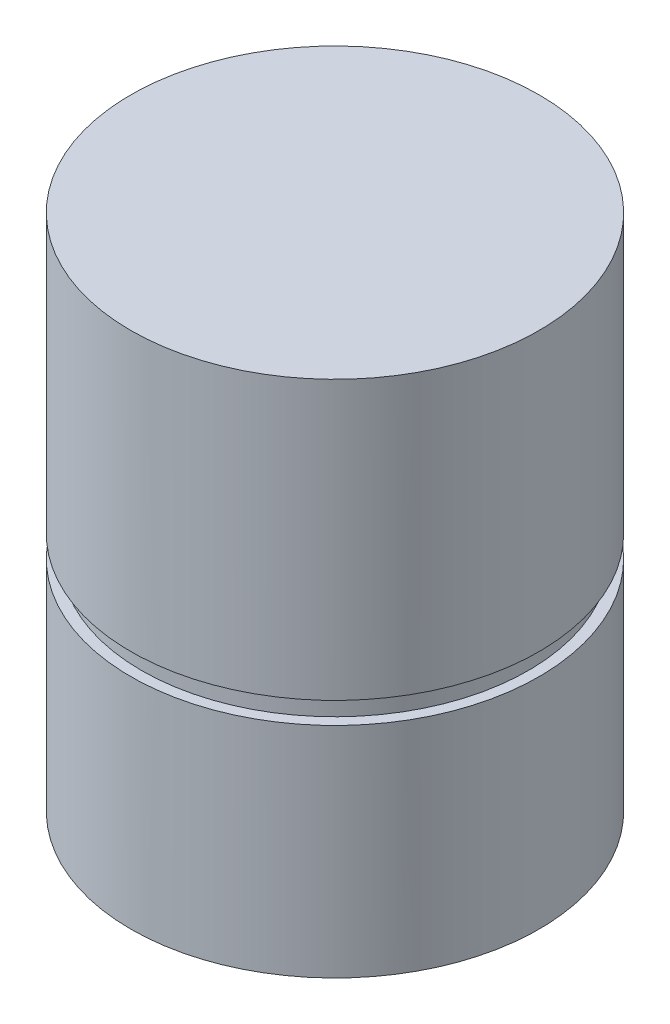
SolidWorks part; units mm, degrees
material "AISI 1020"
ref_plane "Front Plane" through (0, 0, 0) normal (0, 0, 1) x (1, 0, 0)
ref_plane "Top Plane" through (0, 0, 0) normal (0, 1, 0) x (1, 0, 0)
ref_plane "Right Plane" through (0, 0, 0) normal (1, 0, 0) x (0, 0, -1)
sketch "Sketch1" plane through (0, 0, 0) normal (0, 1, 0) x (1, 0, 0)
  circle A0 centre (0, 0) radius 11
extrude "Boss-Extrude1" add sketch "Sketch1" along normal blind 27.94
ref_plane "Plane1" through (0, 12.954, 0) normal (0, 1, 0) x (1, 0, 0)
sketch "Sketch2" plane through (0, 12.954, 0) normal (0, 1, 0) x (1, 0, 0)
  line L0 (-17.2394, 14.5634) -> (-16.2838, -14.8408)
  line L1 (-16.2838, -14.8408) -> (21.4061, -16.2957)
  line L2 (21.4061, -16.2957) -> (22.0943, 14.1973)
  line L3 (22.0943, 14.1973) -> (19.8877, 14.5634)
  circle A0 centre (0, 0) radius 10.4267
  arc A1 (-17.2394, 14.5634) -> (19.8877, 14.5634) centre (1.3242, -556.5965) cw
  dimension "D1" = 20.8534
extrude "Cut-Extrude1" cut sketch "Sketch2" against normal blind 1.1684
